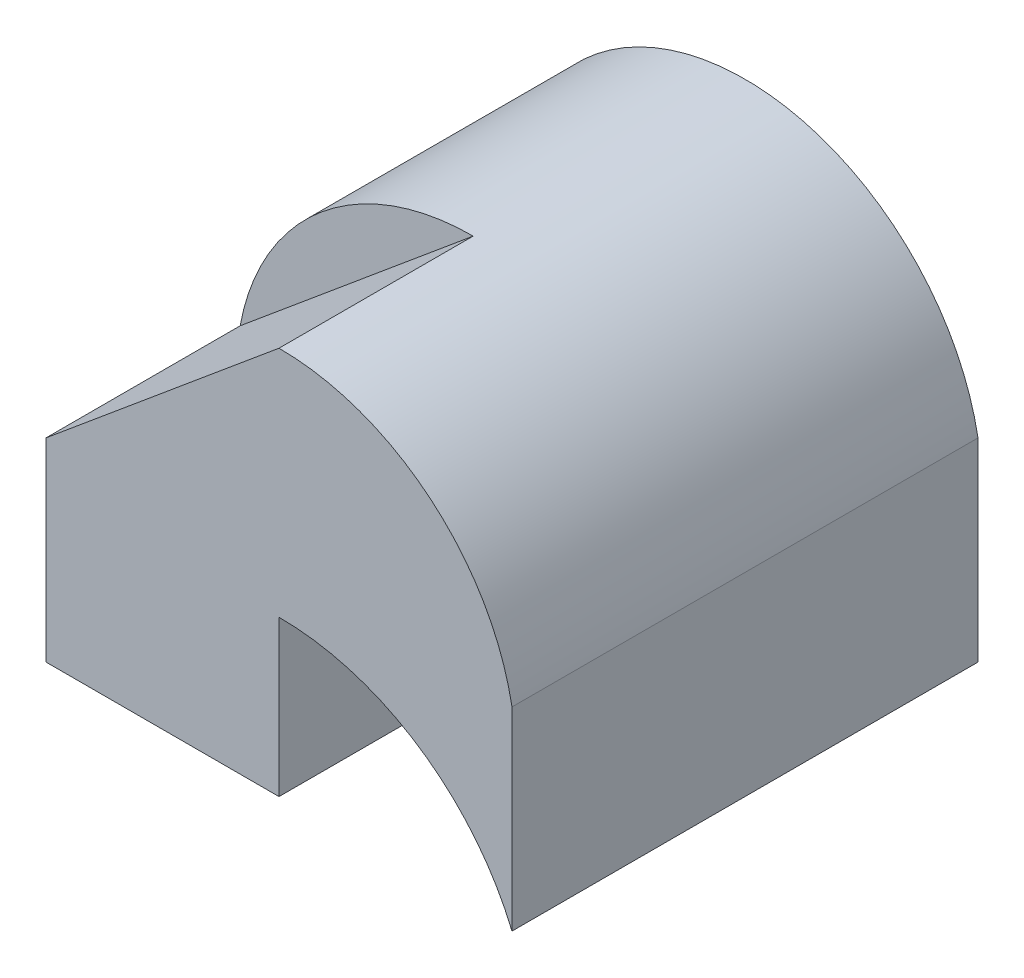
SolidWorks part; units mm, degrees
ref_plane "Front" through (0, 0, 0) normal (0, 0, 1) x (1, 0, 0)
ref_plane "Top" through (0, 0, 0) normal (0, 1, 0) x (1, 0, 0)
ref_plane "Right" through (0, 0, 0) normal (1, 0, 0) x (0, 0, -1)
sketch "Sketch1" plane through (0, 0, 0) normal (0, 1, 0) x (1, 0, 0)
  line L1 (-3, -3) -> (3, -3)
  line L2 (-3, -3) -> (-3, 3)
  line L3 (-3, 3) -> (3, 3)
  line L4 (3, -3) -> (3, 3)
  line L5 (-3, -3) -> (3, 3) construction
  line L6 (-3, 3) -> (3, -3) construction
  point P0 (0, 0)
  dimension "D1" = 6
  dimension "D2" = 6
extrude "Boss-Extrude1" add sketch "Sketch1" along normal blind 5
sketch "Sketch5" plane through (0, 0, 3) normal (0, 0, 1) x (1, 0, 0)
  line L0 (-3, 5) -> (-3, 0) construction
  line L1 (3, 5) -> (3, 0) construction
  line L2 (0, 2) -> (0, 0)
  line L6 (-3, 0) -> (3, 0)
  line L7 (3, 0) -> (3, 5)
  line L8 (3, 5) -> (-3, 5)
  line L9 (-3, 5) -> (-3, 0)
  line L10 (-3, 0) -> (3, 0)
  line L11 (3, 0) -> (3, 5)
  line L12 (3, 5) -> (-3, 5)
  line L13 (-3, 5) -> (-3, 0)
  arc A0 (-3, 0) -> (3, 0) centre (0, -1.25) cw
  arc A1 (-3, 2.5) -> (3, 2.5) centre (0, 1.95) cw
  point P8 (0, 2)
  point P14 (0, 5)
  line M5 (-3, 0) -> (3, 0)
  line M7 (3, 5) -> (-3, 5)
  line M8 (-3, 5) -> (-3, 0)
  dimension "D1" = 2
  dimension "D2" = 5
  dimension "D3" = 0
extrude "Cut-Extrude4" cut sketch "Sketch5" against normal blind 12.5 contours A1 L12 M8 | A1 L11 M7 | A0 L2 M5
sketch "Sketch6" plane through (0, 0, 3) normal (0, 0, 1) x (1, 0, 0)
  line L0 (-3, 2.5) -> (-3, 0) construction
  line L1 (-3, 2) -> (0, 5)
  line L2 (-3, 2) -> (0, 2)
  line L3 (3, 0) -> (3, 2.5)
  line L4 (-3, 2.5) -> (-3, 0)
  line L5 (3, 0) -> (3, 2.5)
  line L6 (-3, 2.5) -> (-3, 0)
  line L7 (-3, 2.5) -> (0, 5)
  line L12 (0, 0) -> (0, 2)
  line L13 (0, 0) -> (0, 2)
  line L14 (-3, 0) -> (0, 0)
  line L15 (-3, 0) -> (0, 0)
  arc A0 (-3, 2) -> (0, 5) centre (-3.55, 5.55) ccw
  arc A4 (3, 2.5) -> (-3, 2.5) centre (0, 1.95) ccw
  arc A5 (3, 0) -> (0, 2) centre (0, -1.25) ccw
  arc A6 (3, 2.5) -> (-3, 2.5) centre (0, 1.95) ccw
  arc A7 (3, 0) -> (0, 2) centre (0, -1.25) ccw
  arc M6 (3, 2.5) -> (-3, 2.5) centre (0, 1.95) ccw
  dimension "D2" = 0
extrude "Cut-Extrude5" cut sketch "Sketch6" against normal blind 2.5 contours L7 M6 | L5 A6 L6 A7
sketch "Sketch7" plane through (0, 0, -3) normal (0, 0, -1) x (-1, 0, 0)
  line L4 (-3, 2.5) -> (-3, 0)
  line L5 (0, 2) -> (0, 0)
  line L6 (0, 0) -> (3, 0)
  line L7 (3, 0) -> (3, 2.5)
  line L9 (0, 2) -> (0, 0)
  line L10 (0, 0) -> (3, 0)
  arc A0 (0, 2) -> (3, 0) centre (0, -1.25) cw
  arc A2 (3, 2.5) -> (-3, 2.5) centre (0, 1.95) ccw
  arc A3 (0, 2) -> (-3, 0) centre (0, -1.25) ccw
  dimension "D1" = 0
extrude "Cut-Extrude6" cut sketch "Sketch7" against normal blind 3.5
